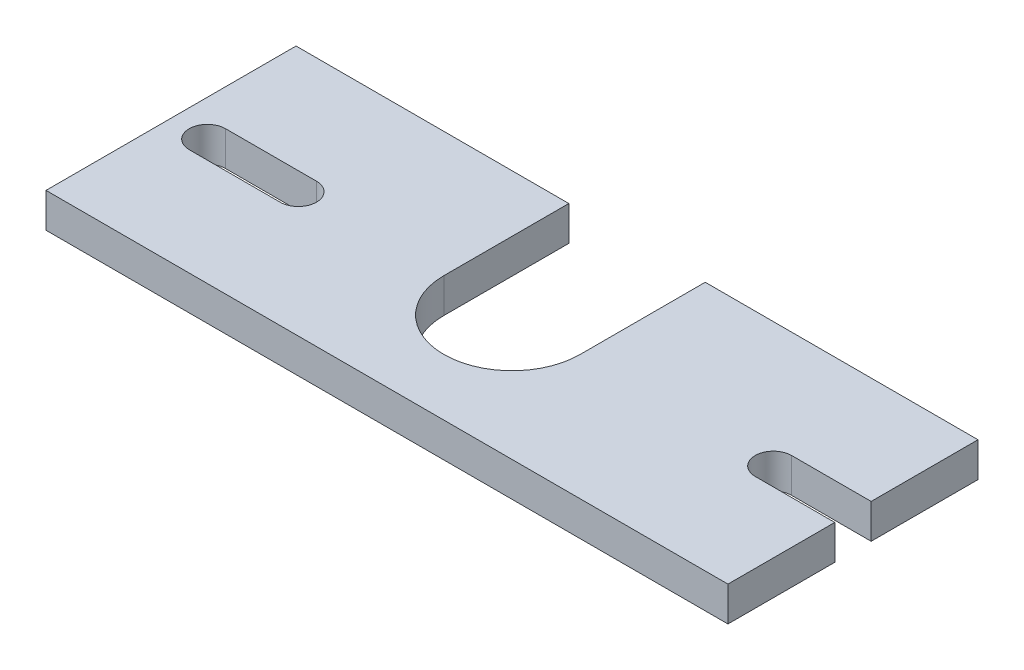
SolidWorks part; units mm, degrees
ref_plane "Front Plane" through (0, 0, 0) normal (0, 0, 1) x (1, 0, 0)
ref_plane "Top Plane" through (0, 0, 0) normal (0, 1, 0) x (1, 0, 0)
ref_plane "Right Plane" through (0, 0, 0) normal (1, 0, 0) x (0, 0, -1)
sketch "Sketch1" plane through (0, 0, 0) normal (0, 1, 0) x (1, 0, 0)
  line L0 (3.2, 11) -> (11.2, 11) construction
  line L1 (0, 0) -> (60, 0)
  line L2 (0, 0) -> (0, 22)
  line L3 (0, 22) -> (24, 22)
  line L4 (60, 0) -> (60, 9.4)
  line L5 (3.2, 12.6) -> (11.2, 12.6)
  line L6 (3.2, 9.4) -> (11.2, 9.4)
  line L7 (53, 11) -> (59.0638, 11) construction
  line L8 (53, 12.6) -> (60, 12.6)
  line L9 (53, 9.4) -> (60, 9.4)
  line L10 (36, 11) -> (36, 22)
  line L11 (60, 12.6) -> (60, 22)
  line L12 (24, 22) -> (24, 11)
  line L13 (36, 22) -> (60, 22)
  arc A0 (3.2, 12.6) -> (3.2, 9.4) centre (3.2, 11) ccw
  arc A1 (11.2, 9.4) -> (11.2, 12.6) centre (11.2, 11) ccw
  arc A2 (53, 12.6) -> (53, 9.4) centre (53, 11) ccw
  arc A4 (24, 11) -> (36, 11) centre (30, 11) ccw
  point P7 (7.2, 11)
  point P12 (59.7766, 11)
  dimension "D3" = 1.6
  dimension "D4" = 1.6
  dimension "D9" = 12
  dimension "D1" = 22
  dimension "D2" = 60
  dimension "D5" = 11
  dimension "D6" = 7
  dimension "D7" = 3.2
  dimension "D8" = 8
  dimension "D10" = 30
extrude "Boss-Extrude1" add sketch "Sketch1" along normal blind 3.04
equation "\"D5@Sketch1\"=\"D1@Sketch1\"/2"
